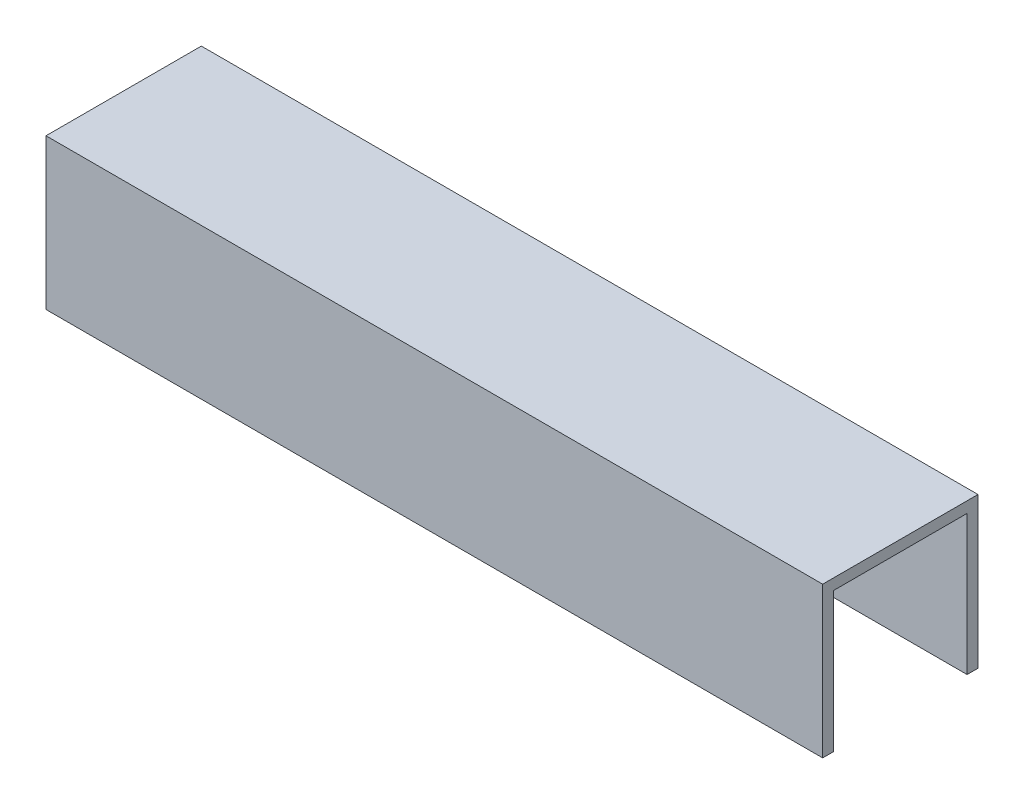
SolidWorks part; units mm, degrees
material "1060 Alloy"
ref_plane "Front Plane" through (0, 0, 0) normal (0, 0, 1) x (1, 0, 0)
ref_plane "Top Plane" through (0, 0, 0) normal (0, 1, 0) x (1, 0, 0)
ref_plane "Right Plane" through (0, 0, 0) normal (1, 0, 0) x (0, 0, -1)
ref_plane "Plane1" through (80, 0, 0) normal (1, 0, 0) x (0, 0, -1)
sketch "Sketch1" plane through (80, 0, 0) normal (1, 0, 0) x (0, 0, -1)
  line L0 (-13.75, 0) -> (-13.75, 28.75)
  line L1 (-13.75, 28.75) -> (13.75, 28.75)
  line L2 (13.75, 28.75) -> (13.75, 0)
  line L3 (13.75, 0) -> (16, 0)
  line L4 (16, 0) -> (16, 31)
  line L5 (16, 31) -> (-16, 31)
  line L6 (-16, 31) -> (-16, 0)
  line L7 (-16, 0) -> (-13.75, 0)
extrude "Boss-Extrude1" add sketch "Sketch1" against normal blind 160
